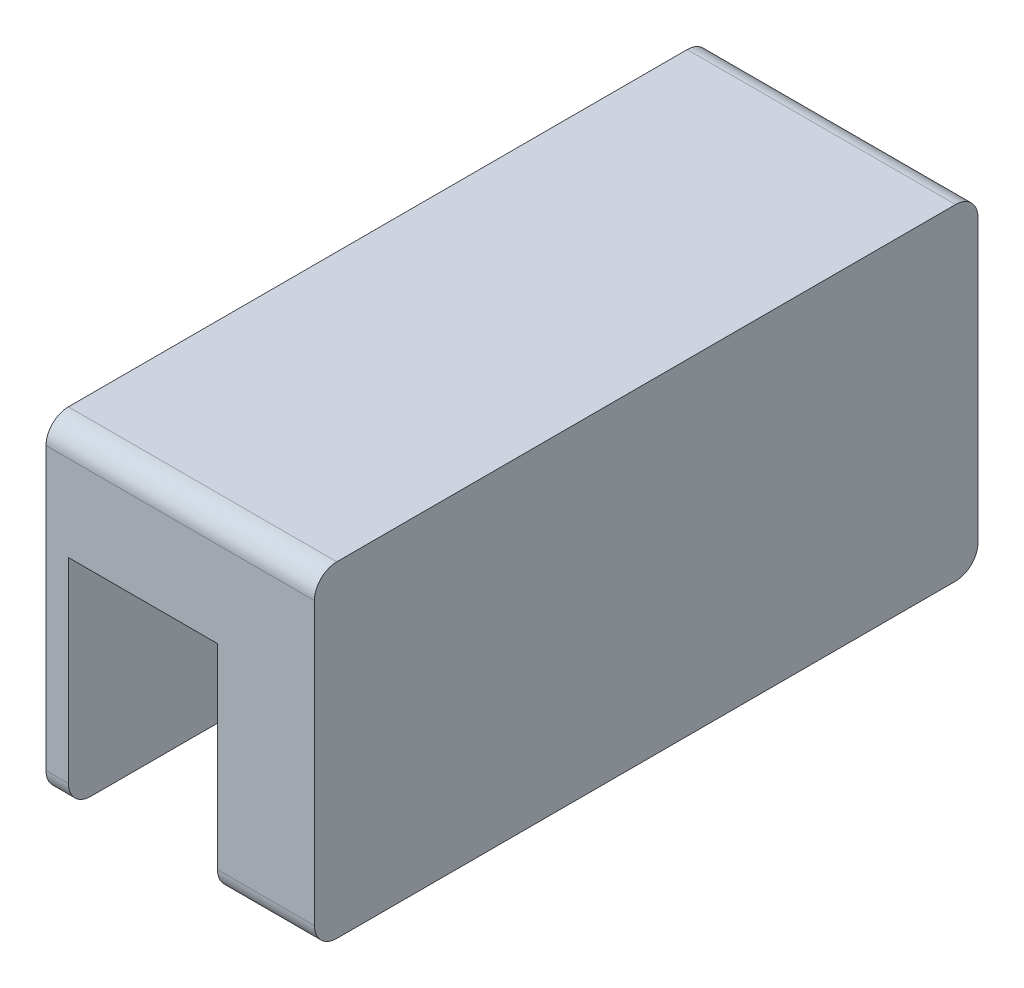
SolidWorks part; units mm, degrees
ref_plane "Plano frontal" through (0, 0, 0) normal (0, 0, 1) x (1, 0, 0)
ref_plane "Plano superior" through (0, 0, 0) normal (0, 1, 0) x (1, 0, 0)
ref_plane "Plano direito" through (0, 0, 0) normal (1, 0, 0) x (0, 0, -1)
sketch "Esboço2" plane through (0, 0, 0) normal (1, 0, 0) x (0, 0, -1)
  line L1 (2.9016, -0.0625) -> (-35.0984, -0.0625) construction
  line L2 (2.9016, -0.0625) -> (-35.0984, -0.0625)
  line L6 (7.6893, -0.0625) -> (2.9016, -0.0625)
  line L8 (-39.8861, -0.0625) -> (-35.0984, -0.0625)
  line L9 (-60.5984, 9.4769) -> (-60.5984, 20.9769)
  line L10 (28.4016, 9.4769) -> (28.4016, 20.9769)
  line L11 (-57.5984, 23.9769) -> (25.4016, 23.9769)
  arc A0 (28.4016, 20.9769) -> (25.4016, 23.9769) centre (25.4016, 20.9769) ccw
  arc A1 (-60.5984, 20.9769) -> (-57.5984, 23.9769) centre (-57.5984, 20.9769) cw
  arc A2 (28.4016, 9.4769) -> (24.5016, 12.3387) centre (25.4016, 9.4769) ccw
  arc A3 (-48.8914, 5.5897) -> (-56.6984, 12.3387) centre (-60.5984, -0.0625) ccw
  arc A4 (-48.8914, 5.5897) -> (-39.8861, -0.0625) centre (-39.8861, 9.9375) ccw
  arc A5 (-60.5984, 9.4769) -> (-56.6984, 12.3387) centre (-57.5984, 9.4769) cw
  arc A6 (16.6946, 5.5897) -> (7.6893, -0.0625) centre (7.6893, 9.9375) cw
  arc A7 (16.6946, 5.5897) -> (24.5016, 12.3387) centre (28.4016, -0.0625) cw
  point P22 (28.4016, 12.9375)
  point P23 (-60.5984, 12.9375)
  dimension "D1" = 3
extrude "Ressalto-extrusão2" add sketch "Esboço2" along normal blind 30
sketch "Esboço3" plane through (0, 0, 0) normal (-1, 0, 0) x (0, 0, 1)
  line L0 (60.5984, 15.2269) -> (60.5984, 20.9769)
  line L1 (60.5984, 20.9769) -> (60.5984, 9.4769) construction
  line L2 (-28.4016, 15.2269) -> (-28.4016, 20.9769)
  line L3 (-28.4016, 9.4769) -> (-28.4016, 20.9769) construction
  line L4 (16.0984, 23.9769) -> (57.5984, 23.9769)
  line L5 (-25.4016, 23.9769) -> (57.5984, 23.9769) construction
  line L6 (16.0984, 23.9769) -> (-25.4016, 23.9769)
  line L7 (60.5984, 15.2269) -> (60.5984, -16.7731)
  line L8 (-28.4016, 15.2269) -> (-28.4016, -16.7731)
  line L9 (57.5984, -19.7731) -> (-25.4016, -19.7731)
  arc A0 (57.5984, 23.9769) -> (60.5984, 20.9769) centre (57.5984, 20.9769) cw
  arc A1 (-28.4016, 20.9769) -> (-25.4016, 23.9769) centre (-25.4016, 20.9769) cw
  arc A2 (-28.4016, -16.7731) -> (-25.4016, -19.7731) centre (-25.4016, -16.7731) ccw
  arc A3 (60.5984, -16.7731) -> (57.5984, -19.7731) centre (57.5984, -16.7731) cw
  dimension "D1" = 3
  dimension "D2" = 3
extrude "Ressalto-extrusão3" add sketch "Esboço3" along normal blind 3
sketch "Esboço4" plane through (30, 0, 0) normal (1, 0, 0) x (0, 0, -1)
  line L0 (-16.0984, 23.9769) -> (25.4016, 23.9769)
  line L1 (25.4016, 23.9769) -> (-57.5984, 23.9769) construction
  line L2 (-16.0984, 23.9769) -> (-57.5984, 23.9769)
  line L3 (28.4016, 15.2269) -> (28.4016, 20.9769)
  line L4 (28.4016, 9.4769) -> (28.4016, 20.9769) construction
  line L5 (-60.5984, 20.9769) -> (-60.5984, 15.2269)
  line L7 (28.4016, 15.2269) -> (28.4016, -16.7731)
  line L8 (28.4016, 9.4769) -> (28.4016, -16.7731) construction
  line L9 (-60.5984, 20.9769) -> (-60.5984, 9.4769) construction
  line L10 (-60.5984, 15.2269) -> (-60.5984, -16.7731)
  line L11 (25.4016, -19.7731) -> (-57.5984, -19.7731)
  arc A0 (25.4016, 23.9769) -> (28.4016, 20.9769) centre (25.4016, 20.9769) cw
  arc A1 (-60.5984, 20.9769) -> (-57.5984, 23.9769) centre (-57.5984, 20.9769) cw
  arc A2 (-60.5984, -16.7731) -> (-57.5984, -19.7731) centre (-57.5984, -16.7731) ccw
  arc A3 (28.4016, -16.7731) -> (25.4016, -19.7731) centre (25.4016, -16.7731) cw
  point P23 (28.4016, -19.7731)
  dimension "D1" = 3
extrude "Ressalto-extrusão4" add sketch "Esboço4" along normal blind 3 and the other way blind 10
